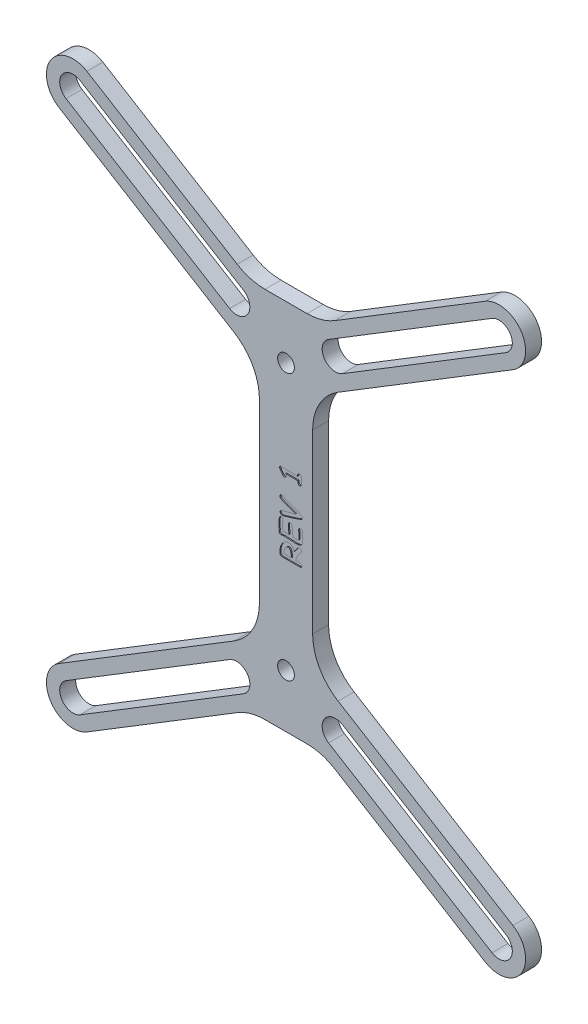
SolidWorks part; units mm, degrees
ref_plane "Front Plane" through (0, 0, 0) normal (0, 0, 1) x (1, 0, 0)
ref_plane "Top Plane" through (0, 0, 0) normal (0, 1, 0) x (1, 0, 0)
ref_plane "Right Plane" through (0, 0, 0) normal (1, 0, 0) x (0, 0, -1)
sketch "Sketch1" plane through (0, 0, 0) normal (0, 0, 1) x (1, 0, 0)
  line L0 (-40.8932, -38.5282) -> (-0.8888, -14.0632) construction
  line L1 (-40.8932, -38.5282) -> (-80.8976, -14.0632) construction
  line L2 (-40.8932, -88.5282) -> (-0.8888, -112.9932) construction
  line L3 (-40.8932, -88.5282) -> (-80.8976, -112.9932) construction
  line L4 (-40.8932, -38.5282) -> (-40.8932, -88.5282) construction
  line L5 (-80.8976, -63.5282) -> (-0.8888, -63.5282) construction
  line L6 (-0.8888, -14.0632) -> (-0.8888, -112.9932) construction
  line L7 (-80.8976, -14.0632) -> (-80.8976, -112.9932) construction
  line L8 (-78.2889, -9.7976) -> (-50.0632, -27.0593)
  line L9 (-44.8459, -28.5282) -> (-36.9405, -28.5282)
  line L10 (-31.7232, -27.0593) -> (-3.4975, -9.7976)
  line L11 (1.7198, -18.3287) -> (-31.1105, -38.4064)
  line L12 (-35.8932, -46.9375) -> (-35.8932, -80.1189)
  line L13 (-31.1105, -88.65) -> (1.7198, -108.7276)
  line L14 (-3.4975, -117.2587) -> (-31.7232, -99.997)
  line L15 (-36.9405, -98.5282) -> (-44.8459, -98.5282)
  line L16 (-50.0632, -99.997) -> (-78.2889, -117.2587)
  line L17 (-83.5062, -108.7276) -> (-50.6759, -88.65)
  line L18 (-45.8932, -80.1189) -> (-45.8932, -46.9375)
  line L19 (-50.6759, -38.4064) -> (-83.5062, -18.3287)
  line L20 (-67.0911, -28.3675) -> (-61.8738, -19.8364) construction
  line L21 (-62.2862, -95.7503) -> (-57.0689, -104.2814) construction
  line L22 (4.1112, -154.3146) -> (4.1112, -80.0894) construction
  line L23 (-80.8976, -112.9932) -> (-50.1855, -94.211) construction
  line L25 (-82.2019, -110.8604) -> (-51.4898, -92.0782)
  line L26 (-79.5932, -115.1259) -> (-48.8812, -96.3437)
  line L27 (-31.6009, -94.211) -> (-0.8888, -112.9932) construction
  line L28 (-30.2966, -92.0782) -> (0.4155, -110.8604)
  line L29 (-32.9052, -96.3437) -> (-2.1932, -115.1259)
  line L30 (-80.8976, -14.0632) -> (-50.1855, -32.8454) construction
  line L31 (-79.5932, -11.9304) -> (-48.8812, -30.7126)
  line L32 (-82.2019, -16.1959) -> (-51.4898, -34.9781)
  line L33 (-0.8888, -14.0632) -> (-31.6009, -32.8454) construction
  line L34 (0.4155, -16.1959) -> (-30.2966, -34.9781)
  line L35 (-2.1932, -11.9304) -> (-32.9052, -30.7126)
  circle A0 centre (-40.8932, -38.5282) radius 2.125 construction
  circle A1 centre (-40.8932, -88.5282) radius 2.125 construction
  circle A2 centre (-40.8932, -38.5282) radius 2.125 construction
  circle A3 centre (-40.8932, -88.5282) radius 2.125 construction
  circle A4 centre (-40.8932, -88.5282) radius 1.575
  circle A5 centre (-40.8932, -38.5282) radius 1.575
  arc A6 (-78.2889, -9.7976) -> (-83.5062, -18.3287) centre (-80.8976, -14.0632) ccw
  arc A7 (1.7198, -18.3287) -> (-3.4975, -9.7976) centre (-0.8888, -14.0632) ccw
  arc A8 (-3.4975, -117.2587) -> (1.7198, -108.7276) centre (-0.8888, -112.9932) ccw
  arc A9 (-83.5062, -108.7276) -> (-78.2889, -117.2587) centre (-80.8976, -112.9932) ccw
  arc A10 (-31.1105, -38.4064) -> (-35.8932, -46.9375) centre (-25.8932, -46.9375) ccw
  arc A11 (-45.8932, -46.9375) -> (-50.6759, -38.4064) centre (-55.8932, -46.9375) ccw
  arc A12 (-50.6759, -88.65) -> (-45.8932, -80.1189) centre (-55.8932, -80.1189) ccw
  arc A13 (-35.8932, -80.1189) -> (-31.1105, -88.65) centre (-25.8932, -80.1189) ccw
  arc A14 (-36.9405, -28.5282) -> (-31.7232, -27.0593) centre (-36.9405, -18.5282) ccw
  arc A15 (-50.0632, -27.0593) -> (-44.8459, -28.5282) centre (-44.8459, -18.5282) ccw
  arc A16 (-31.7232, -99.997) -> (-36.9405, -98.5282) centre (-36.9405, -108.5282) ccw
  arc A17 (-44.8459, -98.5282) -> (-50.0632, -99.997) centre (-44.8459, -108.5282) ccw
  arc A18 (-82.2019, -110.8604) -> (-79.5932, -115.1259) centre (-80.8976, -112.9932) ccw
  arc A19 (-48.8812, -96.3437) -> (-51.4898, -92.0782) centre (-50.1855, -94.211) ccw
  arc A20 (-30.2966, -92.0782) -> (-32.9052, -96.3437) centre (-31.6009, -94.211) ccw
  arc A21 (-2.1932, -115.1259) -> (0.4155, -110.8604) centre (-0.8888, -112.9932) ccw
  arc A22 (-79.5932, -11.9304) -> (-82.2019, -16.1959) centre (-80.8976, -14.0632) ccw
  arc A23 (-51.4898, -34.9781) -> (-48.8812, -30.7126) centre (-50.1855, -32.8454) ccw
  arc A24 (0.4155, -16.1959) -> (-2.1932, -11.9304) centre (-0.8888, -14.0632) ccw
  arc A25 (-32.9052, -30.7126) -> (-30.2966, -34.9781) centre (-31.6009, -32.8454) ccw
  point P8 (-65.5415, -103.6021)
  point P9 (-0.8888, -63.5282)
  point P10 (0, 0)
  point P15 (-40.8932, -63.5282)
  point P17 (-80.8976, -63.5282)
  point P29 (-45.8932, -63.5282)
  point P38 (-40.8932, -98.5282)
  point P39 (-40.8932, -28.5282)
  point P40 (-64.4824, -24.102)
  point P43 (-59.6775, -100.0159)
  point P48 (4.1112, -112.9932)
  point P54 (0, 0)
  point P71 (-16.2449, -103.6021)
  point P72 (0, 0)
  point P81 (-65.5415, -23.4543)
  point P88 (-16.2449, -23.4543)
  point P95 (-72.6647, -108.7276)
  point P96 (-0.8888, -112.9932)
  point P97 (-31.6003, -93.7853)
  point P98 (0, 0)
  point P99 (0, -110.9037)
  point P100 (0, 0)
  point P101 (0, 0)
  point P102 (0, 0)
  point P103 (-207.7436, -26.5583)
  point P104 (0, 0)
  dimension "D1" = 3.15
  dimension "D4" = 10
  dimension "D6" = 10
  dimension "D3" = 10
  dimension "D5" = 10
  dimension "D7" = 10
  dimension "D8" = 36
  dimension "D9" = 2.5
  dimension "D10" = 2.5
  dimension "D11" = 2.5
  dimension "D12" = 2.5
extrude "Boss-Extrude1" add sketch "Sketch1" along normal blind 3
sketch "Sketch3" plane through (0, 0, 3) normal (0, 0, 1) x (1, 0, 0)
  line L0 (-37.9966, -74.3548) -> (-37.9966, -52.7015) construction
  line L1 (-35.8932, -80.1189) -> (-35.8932, -46.9375) construction
  text T0 "<b>REV 1</b>" font "Comic Sans MS" height 4
  point P4 (-35.8932, -63.5282)
  point P5 (-37.9966, -63.5282)
  point P6 (-37.6173, -51.2898)
  point P8 (-38.9687, -53.0069)
  point P9 (0, 0)
  point P10 (0, 0)
  point P11 (-37.9966, -74.3548)
extrude "Cut-Extrude1" cut sketch "Sketch3" against normal blind 0.2
